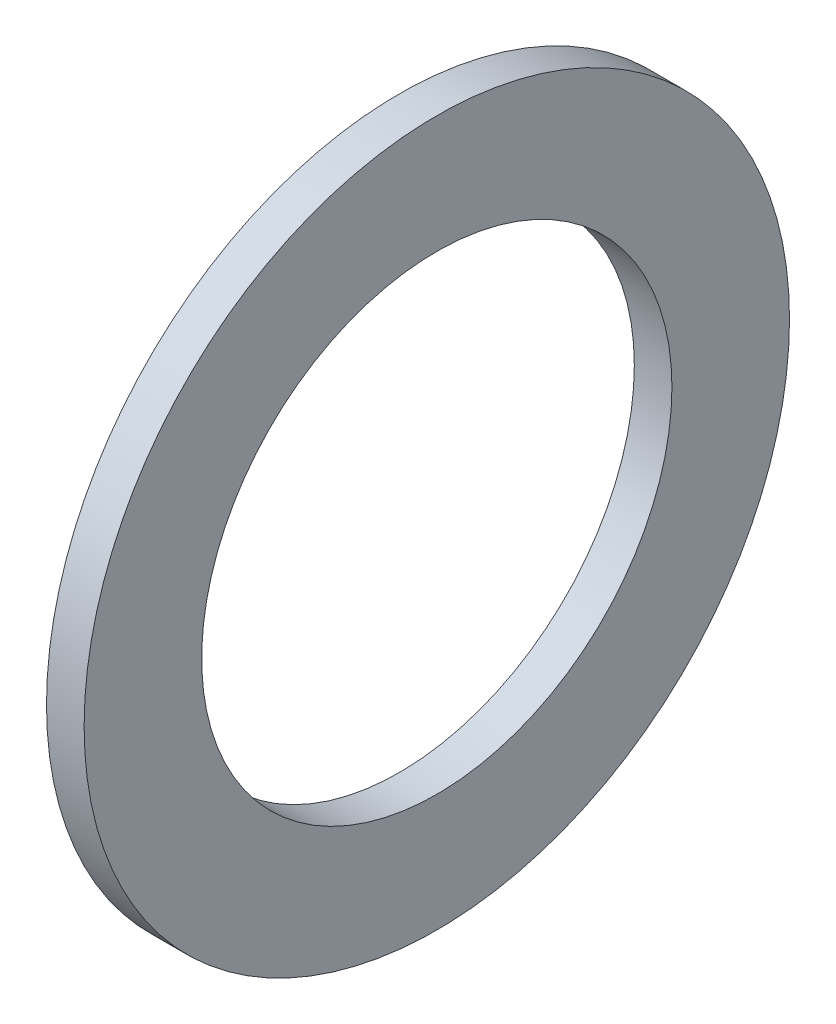
SolidWorks part; units mm, degrees
ref_plane "Front Plane" through (0, 0, 0) normal (0, 0, 1) x (1, 0, 0)
ref_plane "Top Plane" through (0, 0, 0) normal (0, 1, 0) x (1, 0, 0)
ref_plane "Right Plane" through (0, 0, 0) normal (1, 0, 0) x (0, 0, -1)
sketch "Sketch1" plane through (0, 0, 0) normal (1, 0, 0) x (0, 0, -1)
  circle A0 centre (0, 0) radius 4.7625
  circle A1 centre (0, 0) radius 3.175
  dimension "OD" = 9.525
  dimension "ID" = 6.35
extrude "Boss-Extrude1" add sketch "Sketch1" along normal blind 0.508
